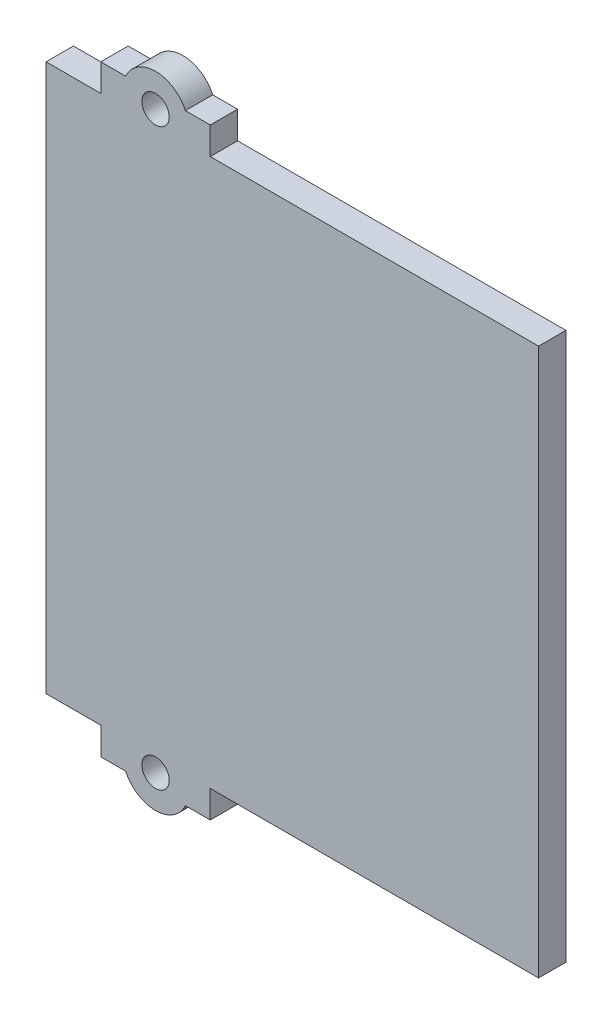
SolidWorks part; units mm, degrees
ref_plane "Front Plane" through (0, 0, 0) normal (0, 0, 1) x (1, 0, 0)
ref_plane "Top Plane" through (0, 0, 0) normal (0, 1, 0) x (1, 0, 0)
ref_plane "Right Plane" through (0, 0, 0) normal (1, 0, 0) x (0, 0, -1)
sketch "Sketch1" plane through (0, 0, 0) normal (0, 0, 1) x (1, 0, 0)
  line L1 (45, 50) -> (-45, 50)
  line L2 (45, 50) -> (45, -50)
  line L3 (45, -50) -> (-45, -50)
  line L4 (-45, 50) -> (-45, -50)
  line L5 (45, 50) -> (-45, -50) construction
  line L6 (45, -50) -> (-45, 50) construction
  point P0 (0, 0)
  dimension "D1" = 90
  dimension "D2" = 100
extrude "Boss-Extrude1" add sketch "Sketch1" along normal blind 5
sketch "Sketch2" plane through (0, 50, 0) normal (0, 1, 0) x (1, 0, 0)
  line L0 (45, -5) -> (-45, -5) construction
  line L1 (-35, -5) -> (-15, -5)
  line L2 (-35, -5) -> (-35, 0)
  line L3 (-35, 0) -> (-15, 0)
  line L4 (-15, -5) -> (-15, 0)
  line L5 (45, 0) -> (-45, 0) construction
  line L6 (-45, -5) -> (-45, 0) construction
  line L8 (45, -5) -> (45, 0) construction
  dimension "D1" = 10
  dimension "D2" = 20
  dimension "D3" = 60
  dimension "D4" = 5
extrude "Boss-Extrude2" add sketch "Sketch2" along normal blind 5
mirror "Mirror1" about plane through (0, 0, 0) normal (0, 1, 0) of "Boss-Extrude2"
sketch "Sketch3" plane through (0, 0, 5) normal (0, 0, 1) x (1, 0, 0)
  line L0 (-35, 55) -> (-15, 55) construction
  line L1 (-35, 50) -> (-45, 50) construction
  line L2 (-15, 55) -> (-15, 50) construction
  line L3 (-35, 55) -> (-35, 50) construction
  circle A0 centre (-25, 52.5) radius 6
  dimension "D1" = 12
  dimension "D2" = 2.5
  dimension "D3" = 10
  dimension "D4" = 2.5
  dimension "D5" = 10
extrude "Boss-Extrude3" add sketch "Sketch3" against normal blind 5
sketch "Sketch4" plane through (0, 0, 5) normal (0, 0, 1) x (1, 0, 0)
  line L0 (-15, 55) -> (-15, 50) construction
  line L1 (-19.5456, 55) -> (-15, 55) construction
  circle A0 centre (-25, 52.5) radius 2.5
  arc A2 (-19.5456, 55) -> (-30.4544, 55) centre (-25, 52.5) ccw construction
  dimension "D1" = 5
  dimension "D2" = 10
  dimension "D3" = 2.5
  dimension "D4" = 3.5
extrude "Cut-Extrude1" cut sketch "Sketch4" against normal blind 5
mirror "Mirror2" about plane through (0, 0, 0) normal (0, 1, 0) of "Boss-Extrude3", "Cut-Extrude1"
